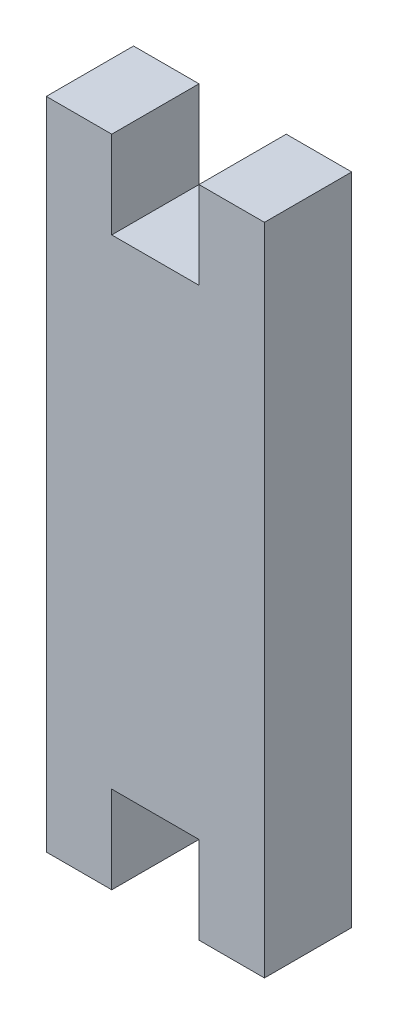
SolidWorks part; units mm, degrees
ref_plane "Front Plane" through (0, 0, 0) normal (0, 0, 1) x (1, 0, 0)
ref_plane "Top Plane" through (0, 0, 0) normal (0, 1, 0) x (1, 0, 0)
ref_plane "Right Plane" through (0, 0, 0) normal (1, 0, 0) x (0, 0, -1)
sketch "Sketch1" plane through (0, 0, 0) normal (0, 0, 1) x (1, 0, 0)
  line L1 (0, 0) -> (10, 0)
  line L2 (0, 0) -> (0, 30)
  line L3 (0, 30) -> (10, 30)
  line L4 (10, 0) -> (10, 30)
  dimension "D1" = 30
  dimension "D2" = 10
extrude "Boss-Extrude1" add sketch "Sketch1" along normal blind 4
sketch "Sketch2" plane through (0, 0, 4) normal (0, 0, 1) x (1, 0, 0)
  line L0 (0, 0) -> (10, 0) construction
  line L1 (7, -4) -> (3, -4)
  line L2 (7, -4) -> (7, 4)
  line L3 (7, 4) -> (3, 4)
  line L4 (3, -4) -> (3, 4)
  line L5 (7, -4) -> (3, 4) construction
  line L6 (7, 4) -> (3, -4) construction
  line L7 (0, 30) -> (0, 0) construction
  point P0 (5, 0)
  dimension "D1" = 3
  dimension "D2" = 4
extrude "Cut-Extrude1" cut sketch "Sketch2" against normal through all
sketch "Sketch3" plane through (0, 0, 0) normal (0, 0, -1) x (-1, 0, 0)
  line L0 (-10, 30) -> (0, 30) construction
  line L1 (-7, 34) -> (-3, 34)
  line L2 (-7, 34) -> (-7, 26)
  line L3 (-7, 26) -> (-3, 26)
  line L4 (-3, 34) -> (-3, 26)
  line L5 (-7, 34) -> (-3, 26) construction
  line L6 (-7, 26) -> (-3, 34) construction
  line L7 (0, 30) -> (0, 0) construction
  point P0 (-5, 30)
  dimension "D1" = 3
  dimension "D2" = 4
extrude "Cut-Extrude2" cut sketch "Sketch3" against normal through all
equation "\"length\"=30"
equation "\"D1@Sketch1\" = \"length\""
equation "\"mat\"=\"mat@V1.assembly\""
equation "\"D1@Boss-Extrude1\"=\"mat\""
equation "\"D2@Sketch2\" = \"mat\""
equation "\"D2@Sketch3\" = \"mat\""
